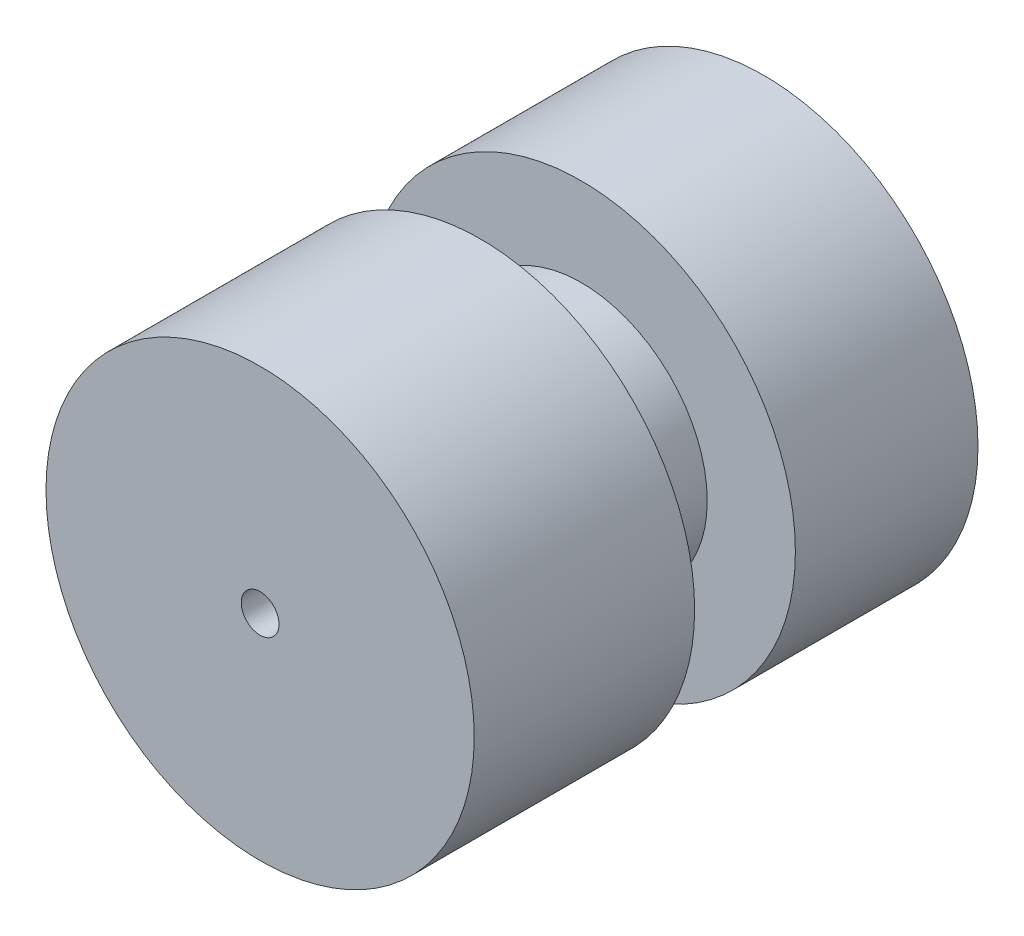
SolidWorks part; units mm, degrees
ref_plane "Front Plane" through (0, 0, 0) normal (0, 0, 1) x (1, 0, 0)
ref_plane "Top Plane" through (0, 0, 0) normal (0, 1, 0) x (1, 0, 0)
ref_plane "Right Plane" through (0, 0, 0) normal (1, 0, 0) x (0, 0, -1)
sketch "Sketch1" plane through (0, 0, 0) normal (0, 0, 1) x (1, 0, 0)
  circle A0 centre (0, 0) radius 17
  circle A1 centre (0, 0) radius 1.5
  dimension "D1" = 34
  dimension "D2" = 3
extrude "Boss-Extrude1" add sketch "Sketch1" along normal blind 40
sketch "Sketch2" plane through (0, 0, 40) normal (0, 0, 1) x (1, 0, 0)
  circle A0 centre (0, 0) radius 10
  circle A1 centre (0, 0) radius 17 construction
  circle A2 centre (0, 0) radius 17
  dimension "D1" = 20
extrude "Cut-Extrude1" cut sketch "Sketch2" against normal blind 8 from offset 17.5 offset against normal yes
